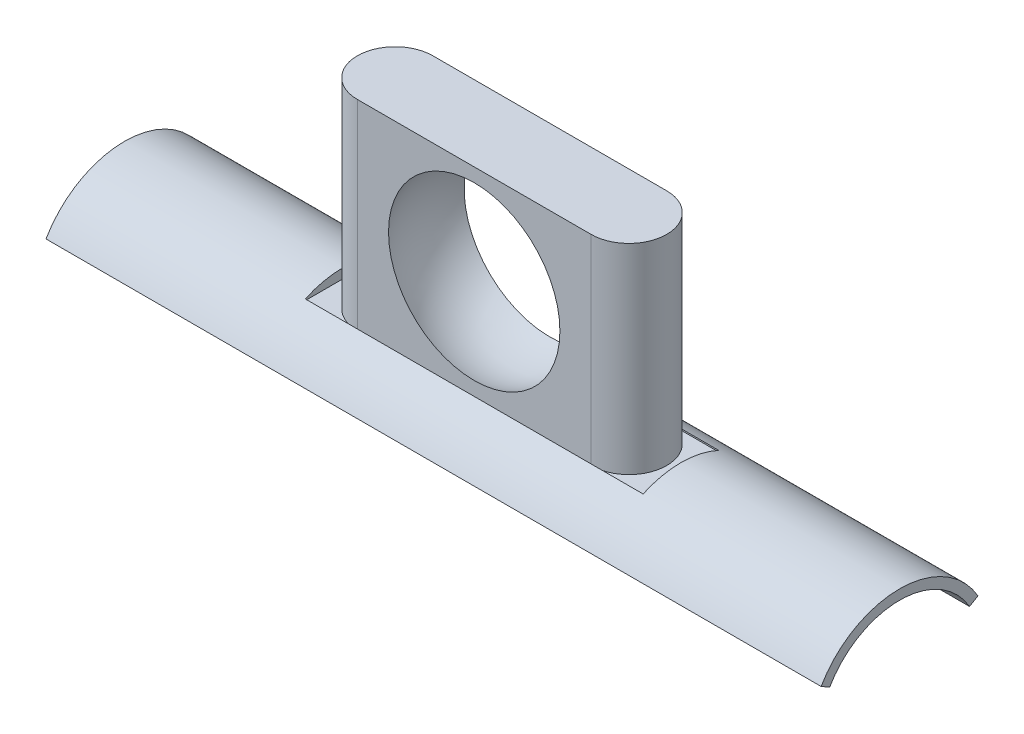
SolidWorks part; units mm, degrees
material "6061-T6 (SS)"
ref_plane "Front Plane" through (0, 0, 0) normal (0, 0, 1) x (1, 0, 0)
ref_plane "Top Plane" through (0, 0, 0) normal (0, 1, 0) x (1, 0, 0)
ref_plane "Right Plane" through (0, 0, 0) normal (1, 0, 0) x (0, 0, -1)
sketch "Sketch3" plane through (0, 0, 0) normal (1, 0, 0) x (0, 0, -1)
  line L0 (-27.4963, 15.875) -> (-30.8509, 17.8117)
  line L1 (27.4963, 15.875) -> (30.8509, 17.8117)
  arc A0 (30.8509, 17.8117) -> (-30.8509, 17.8117) centre (0, 0) ccw
  arc A1 (27.4963, 15.875) -> (-27.4963, 15.875) centre (0, 0) ccw
  dimension "D1" = 71.247
  dimension "D2" = 63.5
  dimension "D3" = 120
extrude "Boss-Extrude2" add sketch "Sketch3" along normal mid plane 304.8
ref_plane "Plane1" through (0, 35.6235, 0) normal (0, 1, 0) x (1, 0, 0)
sketch "Sketch6" plane through (0, 35.6235, 0) normal (0, 1, 0) x (1, 0, 0)
  line L1 (-66.421, -14.859) -> (66.421, -14.859)
  line L2 (-66.421, -14.859) -> (-66.421, 14.859)
  line L3 (-66.421, 14.859) -> (66.421, 14.859)
  line L4 (66.421, -14.859) -> (66.421, 14.859)
  dimension "D1" = 132.842
  dimension "D2" = 29.718
  dimension "D3" = 14.859
  dimension "D4" = 66.421
extrude "Cut-Extrude1" cut sketch "Sketch6" against normal blind 3.81
sketch "Sketch8" plane through (0, 31.8135, 0) normal (0, 1, 0) x (1, 0, 0)
  line L0 (-45.974, 0) -> (45.974, 0) construction
  line L1 (-45.974, 14.859) -> (45.974, 14.859)
  line L2 (-45.974, -14.859) -> (45.974, -14.859)
  arc A0 (-45.974, 14.859) -> (-45.974, -14.859) centre (-45.974, 0) ccw
  arc A1 (45.974, -14.859) -> (45.974, 14.859) centre (45.974, 0) ccw
  point P2 (0, 0)
  point P7 (-60.833, 0)
  point P8 (60.833, 0)
  dimension "D1" = 121.666
  dimension "D2" = 29.718
extrude "Boss-Extrude3" add sketch "Sketch8" along normal blind 78.74
sketch "Sketch9" plane through (0, 0, 0) normal (0, 0, 1) x (1, 0, 0)
  line L0 (-45.974, 32.3766) -> (45.974, 32.3766) construction
  line L1 (0, 108.3226) -> (0, 34.6626)
  line L2 (-45.974, 110.5535) -> (-45.974, 32.3766) construction
  arc A0 (0, 34.6626) -> (0, 108.3226) centre (0, 71.4926) ccw
  dimension "D1" = 73.66
  dimension "D2" = 39.116
  dimension "D3" = 45.974
revolve "Cut-Revolve1" cut sketch "Sketch9" angle 360 about L1
